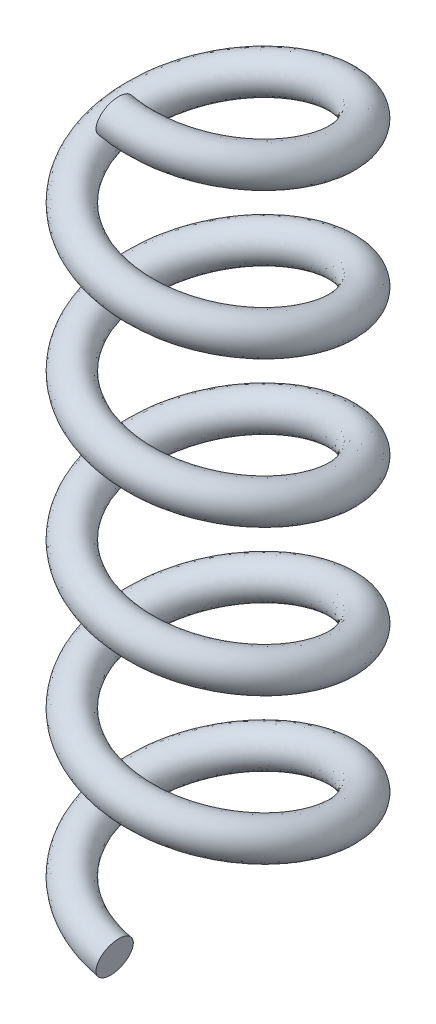
SolidWorks part; units mm, degrees
ref_plane "Přední rovina" through (0, 0, 0) normal (0, 0, 1) x (1, 0, 0)
ref_plane "Horní rovina" through (0, 0, 0) normal (0, 1, 0) x (1, 0, 0)
ref_plane "Pravá rovina" through (0, 0, 0) normal (1, 0, 0) x (0, 0, -1)
sketch "Skica2" plane through (0, 0, 0) normal (0, 1, 0) x (1, 0, 0)
  circle A0 centre (0, 0) radius 42.5
  dimension "D1" = 85
curve "Šroubovice/spirála1" pitch 60 height 300 turns 5
ref_plane "Rovina1" through (0, 0, 42.5) normal (-0.9757, 0.2192, 0) x (0, 0, 1)
sketch "Skica3" plane through (0, 0, 42.5) normal (-0.9757, 0.2192, 0) x (0, 0, 1)
  circle A0 centre (0, 0) radius 7.5
  dimension "D1" = 15
sweep "Táhnout po křivce1" add profiles "Skica3" path "Šroubovice/spirála1"
